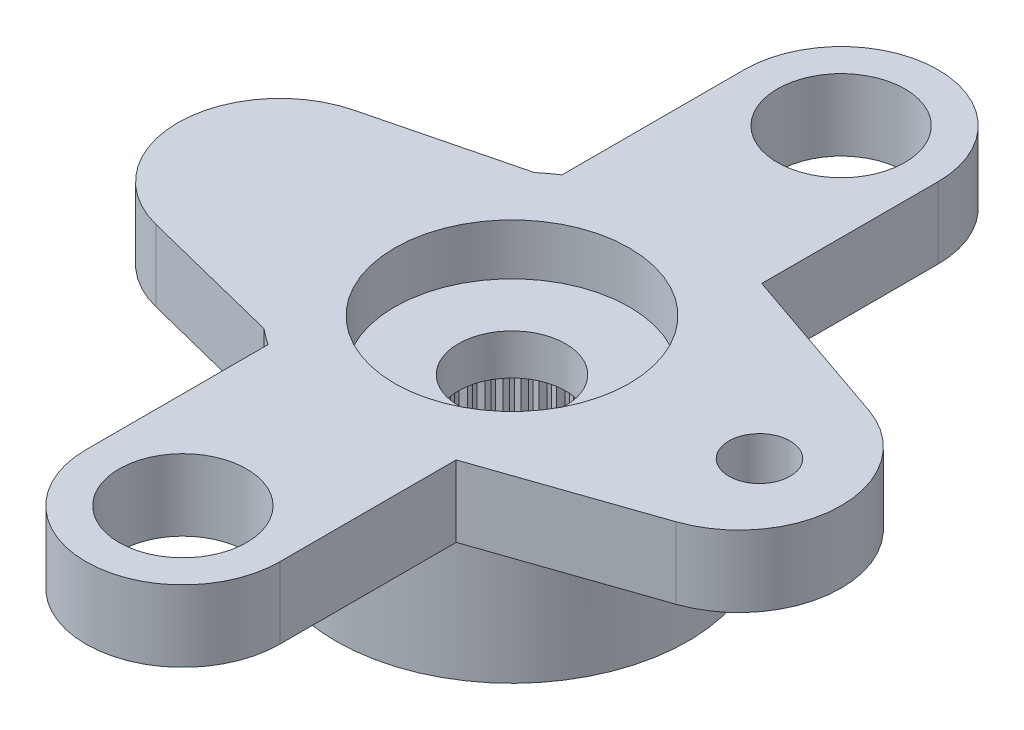
SolidWorks part; units mm, degrees
material "PVC Rígido"
ref_plane "Plano frontal" through (0, 0, 0) normal (0, 0, 1) x (1, 0, 0)
ref_plane "Plano superior" through (0, 0, 0) normal (0, 1, 0) x (1, 0, 0)
ref_plane "Plano direito" through (0, 0, 0) normal (1, 0, 0) x (0, 0, -1)
sketch "Esboço1" plane through (0, 0, 0) normal (0, 1, 0) x (1, 0, 0)
  line L0 (0, 0) -> (-4.55, 0) construction
  line L1 (-5.0371, 1.9398) -> (-2.2091, 2.65)
  line L2 (-2.2091, -2.65) -> (-5.0371, -1.9398)
  arc A0 (-2.2091, -2.65) -> (-2.2091, 2.65) centre (0, 0) ccw
  arc A1 (-5.0371, 1.9398) -> (-5.0371, -1.9398) centre (-4.55, 0) ccw
  dimension "D1" = 6.9
  dimension "D2" = 4
  dimension "D3" = 10
  dimension "D4" = 5.3
extrude "Ressalto-extrusão1" add sketch "Esboço1" against normal blind 1.4
sketch "Esboço2" plane through (0, -1.4, 0) normal (0, -1, 0) x (1, 0, 0)
  arc A0 (-2.2091, -2.65) -> (-2.2091, 2.65) centre (0, 0) ccw construction
  circle A1 centre (0, 0) radius 3.45
extrude "Ressalto-extrusão2" add sketch "Esboço2" along normal offset from surface (2.4 mm away) 3.8 up to face at (-2.5866, 0, 0)
hole_wizard "Furo1" [suppressed] positions "Esboço9" profile "Esboço10" legacy
sketch "Esboço9" plane through (0, 0, 0) normal (0, 1, 0) x (1, 0, 0)
  line L1 (-4.95, 0) -> (0, 0) construction
  arc A2 (-5.0371, 1.9398) -> (-5.0371, -1.9398) centre (-4.55, 0) ccw construction
  point P0 (-4.95, 0)
  point P19 (-6.55, 0)
  dimension "D1" = 1.6
sketch "Esboço10" plane through (-4.95, 0, 0) normal (1, 0, 0) x (0, 0, 1)
  line L0 (0, 0) -> (0, 3.8)
  line L1 (0, 3.8) -> (0.6, 3.8)
  line L2 (0.6, 3.8) -> (0.6, 0)
  line L3 (0.6, 0) -> (0, 0)
  line L4 (0, 110) -> (0, -10) construction
  dimension "Diameter" = 1.2
  dimension "Depth" = 3.8
pattern_linear "Padrão linear1" [suppressed] count 6 spacing 2 along (1, 0, 0)
sketch "Esboço12" plane through (0, 0, 0) normal (0, 1, 0) x (1, 0, 0)
  line L0 (1.1242, 3.2617) -> (5.1017, 1.8908)
  line L1 (5.1017, -1.8908) -> (1.1242, -3.2617)
  arc A0 (-2.2091, -2.65) -> (-2.2091, 2.65) centre (0, 0) ccw construction
  arc A1 (1.1242, -3.2617) -> (1.1242, 3.2617) centre (0, 0) ccw
  arc A2 (5.1017, 1.8908) -> (5.1017, -1.8908) centre (4.45, 0) cw
  arc A3 (-5.0371, 1.9398) -> (-5.0371, -1.9398) centre (-4.55, 0) ccw construction
  dimension "D1" = 2
  dimension "D2" = 13
extrude "Ressalto-extrusão3" add sketch "Esboço12" against normal up to surface (1.4 mm away) up to face at (-4.3116, -1.4, 0)
hole_wizard "Furo2" positions "Esboço13" profile "Esboço14" legacy end condition through all
sketch "Esboço13" plane through (0, 0, 0) normal (0, 1, 0) x (1, 0, 0)
  line L0 (0, 0) -> (4.85, 0) construction
  arc A0 (5.1017, -1.8908) -> (5.1017, 1.8908) centre (4.45, 0) ccw construction
  point P0 (4.85, 0)
  point P6 (6.45, 0)
  dimension "D1" = 1.6
sketch "Esboço14" plane through (4.85, 0, 0) normal (1, 0, 0) x (0, 0, 1)
  line L0 (0, 0) -> (0, 3.8)
  line L1 (0, 3.8) -> (0.6, 3.8)
  line L2 (0.6, 3.8) -> (0.6, 0)
  line L3 (0.6, 0) -> (0, 0)
  line L4 (0, 110) -> (0, -10) construction
  dimension "Diameter" = 1.2
  dimension "Depth" = 3.8
pattern_linear "Padrão linear2" [suppressed] count 7 spacing 2 along (1, 0, 0)
sketch "Esboço16" plane through (0, 0, 0) normal (0, 1, 0) x (1, 0, 0)
  line L0 (0, -6.45) -> (0, 6.45) construction
  line L1 (-1.9, -6.45) -> (-1.9, 6.45)
  line L2 (1.9, -6.45) -> (1.9, 6.45)
  arc A0 (-1.9, -6.45) -> (1.9, -6.45) centre (0, -6.45) ccw
  arc A1 (1.9, 6.45) -> (-1.9, 6.45) centre (0, 6.45) ccw
  point P2 (0, 0)
  dimension "D2" = 16.7
  dimension "D1" = 3.8
extrude "Ressalto-extrusão4" add sketch "Esboço16" against normal up to surface (1.4 mm away) up to face at (4.85, -1.4, 0.6)
hole_wizard "Furo3" positions "Esboço17" profile "Esboço18" legacy end condition through all
sketch "Esboço17" plane through (0, 0, 0) normal (0, 1, 0) x (1, 0, 0)
  point P0 (0, -6.45)
sketch "Esboço18" plane through (0, 0, 6.45) normal (1, 0, 0) x (0, 0, 1)
  line L0 (0, 0) -> (0, 3.8)
  line L1 (0, 3.8) -> (1.25, 3.8)
  line L2 (1.25, 3.8) -> (1.25, 0)
  line L3 (1.25, 0) -> (0, 0)
  line L4 (0, 110) -> (0, -10) construction
  dimension "Diameter" = 2.5
  dimension "Depth" = 3.8
pattern_linear "Padrão linear3" [suppressed] count 2 spacing 2
pattern_circular "PadrãoCircular1" count 2 over 360 about axis through (0, 0, 0) along (0, 1, 0) of "Furo3"
hole_wizard "Furo4" positions "Esboço3" profile "Esboço4" legacy
sketch "Esboço3" plane through (0, -3.8, 0) normal (0, -1, 0) x (-1, 0, 0)
  point P0 (0, 0)
sketch "Esboço4" plane through (0, -3.8, 0) normal (1, 0, 0) x (0, 0, -1)
  line L0 (0, 0) -> (0, 2)
  line L1 (0, 2) -> (2.475, 2)
  line L2 (2.475, 2) -> (2.475, 0)
  line L3 (2.475, 0) -> (0, 0)
  line L4 (0, 110) -> (0, -10) construction
  dimension "Diameter" = 4.95
  dimension "Depth" = 2
hole_wizard "Furo5" positions "Esboço5" profile "Esboço6" legacy
sketch "Esboço5" plane through (0, 0, 0) normal (0, 1, 0) x (1, 0, 0)
  point P0 (0, 0)
sketch "Esboço6" plane through (0, 0, 0) normal (1, 0, 0) x (0, 0, 1)
  line L0 (0, 0) -> (0, 1)
  line L1 (0, 1) -> (2.3, 1)
  line L2 (2.3, 1) -> (2.3, 0)
  line L3 (2.3, 0) -> (0, 0)
  line L4 (0, 110) -> (0, -10) construction
  dimension "Diameter" = 4.6
  dimension "Depth" = 1
hole_wizard "Furo6" positions "Esboço7" profile "Esboço8" legacy end condition through all
sketch "Esboço7" plane through (0, 0, 0) normal (0, 1, 0) x (1, 0, 0)
  point P0 (0, 0)
sketch "Esboço8" plane through (0, 0, 0) normal (1, 0, 0) x (0, 0, 1)
  line L0 (0, 0) -> (0, 3.8)
  line L1 (0, 3.8) -> (1.05, 3.8)
  line L2 (1.05, 3.8) -> (1.05, 0)
  line L3 (1.05, 0) -> (0, 0)
  line L4 (0, 110) -> (0, -10) construction
  dimension "Diameter" = 2.1
  dimension "Depth" = 3.8
sketch "Esboço11" plane through (0, -3.8, 0) normal (0, -1, 0) x (1, 0, 0)
  line L0 (-0.0981, 2.4731) -> (0, 2.375)
  line L1 (0, 2.375) -> (0.0981, 2.4731)
  line L2 (0, 0) -> (0, 2.475) construction
  circle A0 centre (0, 0) radius 2.375 construction
  circle A1 centre (0, 0) radius 2.475
  arc A2 (0.0981, 2.4731) -> (-0.0981, 2.4731) centre (0, 0) ccw
  dimension "D3" = 4.75
  dimension "D2" = 0.1
  dimension "D1" = 0
extrude "Ressalto-extrusão5" add sketch "Esboço11" against normal up to surface (2 mm away) up to face at (0, -1.8, 1.05)
pattern_circular "PadrãoCircular2" count 60 over 360 about axis through (0, 0, 0) along (0, 1, 0) of "Ressalto-extrusão5"
